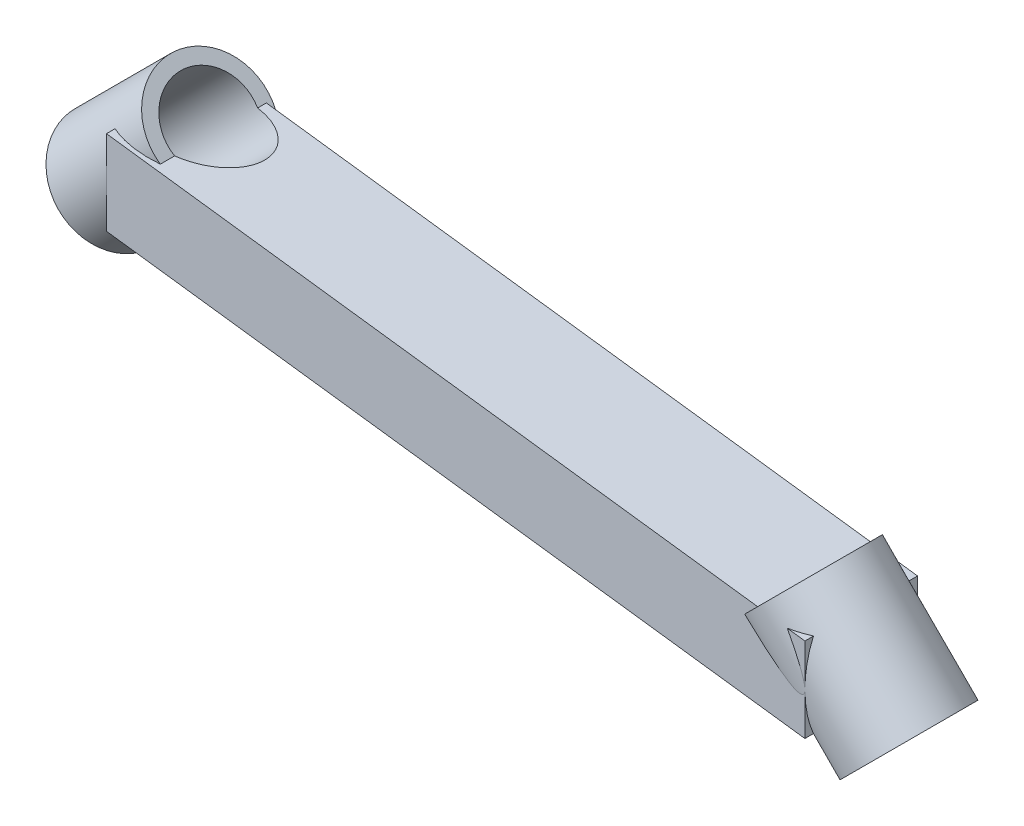
SolidWorks part; units mm, degrees
material "ABS"
ref_plane "Front Plane" through (0, 0, 0) normal (0, 0, 1) x (1, 0, 0)
ref_plane "Top Plane" through (0, 0, 0) normal (0, 1, 0) x (1, 0, 0)
ref_plane "Right Plane" through (0, 0, 0) normal (1, 0, 0) x (0, 0, -1)
sketch "Sketch1" plane through (0, 0, 0) normal (0, 1, 0) x (1, 0, 0)
  line L0 (-70, 0) -> (70, 0) construction
  line L1 (-70, 0) -> (-70, 8) construction
  line L2 (70, 0) -> (70, -8) construction
  line L3 (-70, -2) -> (-70, 18)
  line L6 (70, 2) -> (70, -18)
  line L11 (-70, -2) -> (70, -18)
  line L12 (-70, 18) -> (70, 2)
  point P3 (0, 0)
  dimension "D3" = 8
  dimension "D4" = 10
  dimension "D1" = 140
  dimension "D2" = 8
  dimension "D5" = 10
  dimension "D6" = 10
  dimension "D7" = 10
  dimension "D8" = 20
  dimension "D9" = 20
extrude "Boss-Extrude1" add sketch "Sketch1" against normal mid plane 15
ref_plane "Plane1" through (-35, -35, 0) normal (-0.7071, -0.7071, 0) x (0, 0, 1)
ref_plane "Plane2" through (35, -35, 0) normal (0.7071, -0.7071, 0) x (0, 0, 1)
sketch "Sketch2" plane through (-35, -35, 0) normal (-0.7071, -0.7071, 0) x (0, 0, 1)
  circle A0 centre (-8, 49.4975) radius 10
  dimension "D1" = 20
extrude "Boss-Extrude2" add sketch "Sketch2" along normal mid plane 24
sketch "Sketch3" plane through (35, -35, 0) normal (0.7071, -0.7071, 0) x (0, 0, 1)
  circle A0 centre (8, -49.4975) radius 10
  dimension "D1" = 20
extrude "Boss-Extrude3" add sketch "Sketch3" along normal mid plane 24
sketch "Sketch4" plane through (-43.4853, -43.4853, 0) normal (-0.7071, -0.7071, 0) x (0, 0, 1)
  circle A0 centre (-8, 49.4975) radius 7.5
  circle A1 centre (-8, 49.4975) radius 10 construction
  dimension "D1" = 15
extrude "Cut-Extrude1" cut sketch "Sketch4" against normal through all both and the other way through all
